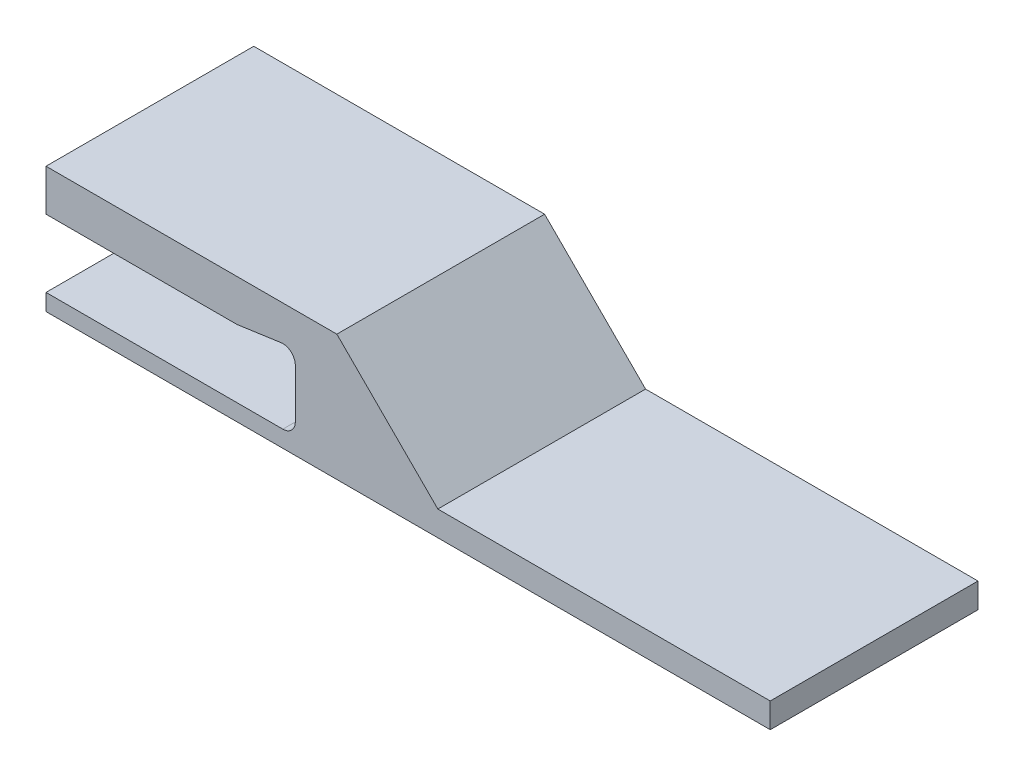
SolidWorks part; units mm, degrees
ref_plane "Front Plane" through (0, 0, 0) normal (0, 0, 1) x (1, 0, 0)
ref_plane "Top Plane" through (0, 0, 0) normal (0, 1, 0) x (1, 0, 0)
ref_plane "Right Plane" through (0, 0, 0) normal (1, 0, 0) x (0, 0, -1)
sketch "Sketch1" plane through (0, 0, 0) normal (0, 0, 1) x (1, 0, 0)
  line L0 (0, 0) -> (0, 4)
  line L1 (0, 4) -> (57, 4)
  line L2 (60, 7) -> (60, 18.841)
  line L3 (56.5757, 21.8108) -> (46.2111, 20.3302)
  line L4 (45.7868, 20.3) -> (0, 20.3)
  line L5 (0, 20.3) -> (0, 30.3)
  line L6 (0, 30.3) -> (70, 30.3)
  line L7 (70, 30.3) -> (94.3, 6)
  line L8 (94.3, 6) -> (174.3, 6)
  line L9 (174.3, 6) -> (174.3, 0)
  line L10 (174.3, 0) -> (0, 0)
  arc A0 (46.2111, 20.3302) -> (45.7868, 20.3) centre (45.7868, 23.3) cw
  arc A1 (60, 18.841) -> (56.5757, 21.8108) centre (57, 18.841) ccw
  arc A2 (57, 4) -> (60, 7) centre (57, 7) ccw
  point P14 (46, 20.3)
  point P17 (60, 22.3)
  dimension "D5" = 3
  dimension "D1" = 16.3
  dimension "D2" = 4
  dimension "D3" = 2
  dimension "D4" = 14
  dimension "D6" = 60
  dimension "D7" = 10
  dimension "D8" = 10
  dimension "D9" = 6
  dimension "D10" = 45
  dimension "D11" = 80
extrude "Boss-Extrude1" add sketch "Sketch1" along normal blind 50
